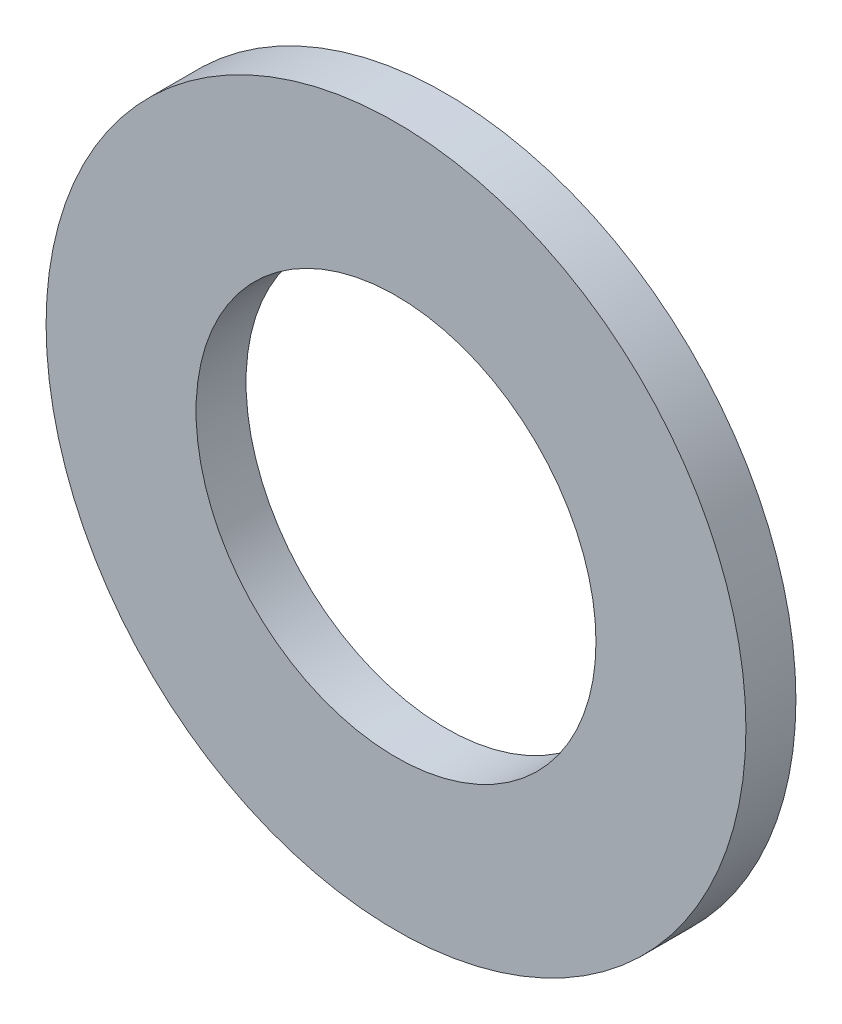
SolidWorks part; units mm, degrees
ref_plane "前视基准面" through (0, 0, 0) normal (0, 0, 1) x (1, 0, 0)
ref_plane "上视基准面" through (0, 0, 0) normal (0, 1, 0) x (1, 0, 0)
ref_plane "右视基准面" through (0, 0, 0) normal (1, 0, 0) x (0, 0, -1)
sketch "草图1" plane through (0, 0, 0) normal (0, 0, 1) x (1, 0, 0)
  circle A0 centre (0, 0) radius 3.5
  circle A1 centre (0, 0) radius 2
  dimension "D1" = 7
  dimension "D2" = 4
extrude "凸台-拉伸1" add sketch "草图1" along normal blind 0.5
